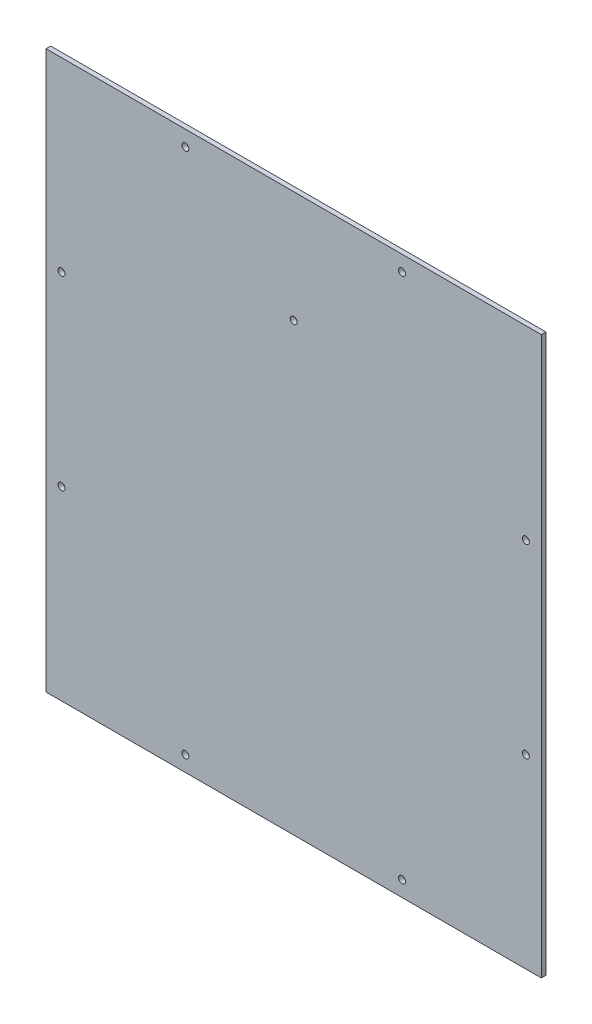
SolidWorks part; units mm, degrees
ref_plane "Спереди" through (0, 0, 0) normal (0, 0, 1) x (1, 0, 0)
ref_plane "Сверху" through (0, 0, 0) normal (0, 1, 0) x (1, 0, 0)
ref_plane "Справа" through (0, 0, 0) normal (1, 0, 0) x (0, 0, -1)
sketch "Эскиз1" plane through (0, 0, 0) normal (0, 0, 1) x (1, 0, 0)
  line L0 (0, 0) -> (320, 0)
  line L1 (0, 0) -> (0, 360)
  line L2 (320, 0) -> (320, 360)
  line L3 (0, 360) -> (320, 360)
  line L4 (10, 350) -> (310, 350) construction
  line L5 (10, 350) -> (10, 10) construction
  line L6 (310, 350) -> (310, 10) construction
  line L7 (10, 10) -> (310, 10) construction
  line L8 (90, 350) -> (90, 10) construction
  line L9 (230, 350) -> (230, 10) construction
  line L10 (10, 240) -> (310, 240) construction
  line L11 (10, 120) -> (310, 120) construction
  line L12 (160, 350) -> (160, 10) construction
  line L13 (0, 0) -> (20, 0) construction
  line L14 (0, 0) -> (0, 20) construction
  line L15 (20, 0) -> (20, 20) construction
  line L16 (0, 20) -> (20, 20) construction
  line L17 (320, 360) -> (300, 360) construction
  line L18 (320, 360) -> (320, 340) construction
  line L19 (300, 360) -> (300, 340) construction
  line L20 (320, 340) -> (300, 340) construction
  circle A0 centre (90, 350) radius 2.25
  circle A1 centre (230, 350) radius 2.25
  circle A2 centre (10, 240) radius 2.25
  circle A3 centre (10, 120) radius 2.25
  circle A4 centre (310, 240) radius 2.25
  circle A5 centre (310, 120) radius 2.25
  circle A6 centre (90, 10) radius 2.25
  circle A7 centre (230, 10) radius 2.25
  dimension "D9" = 4.5
  dimension "D10" = 4.5
  dimension "D11" = 4.5
  dimension "D12" = 120
  dimension "D13" = 4.5
  dimension "D14" = 120
  dimension "D15" = 4.5
  dimension "D16" = 4.5
  dimension "D20" = 4.5
  dimension "D17" = 4.5
  dimension "D1" = 360
  dimension "D2" = 320
  dimension "D3" = 90
  dimension "D4" = 10
  dimension "D5" = 10
  dimension "D6" = 10
  dimension "D7" = 10
  dimension "D8" = 90
  dimension "D18" = 20
  dimension "D19" = 20
  dimension "D28" = 20
  dimension "D29" = 20
extrude "Бобышка-Вытянуть1" add sketch "Эскиз1" along normal blind 3
sketch "Эскиз2" plane through (0, 0, 3) normal (0, 0, 1) x (1, 0, 0)
  line L0 (0, 298) -> (320, 298) construction
  line L1 (0, 360) -> (0, 0) construction
  line L2 (320, 0) -> (320, 360) construction
  line L3 (320, 360) -> (0, 360) construction
  line L4 (0, 288) -> (320, 288) construction
  circle A0 centre (160, 288) radius 2.25
  dimension "D3" = 4.5
  dimension "D1" = 62
  dimension "D2" = 10
extrude "Вырез-Вытянуть1" cut sketch "Эскиз2" against normal through all
